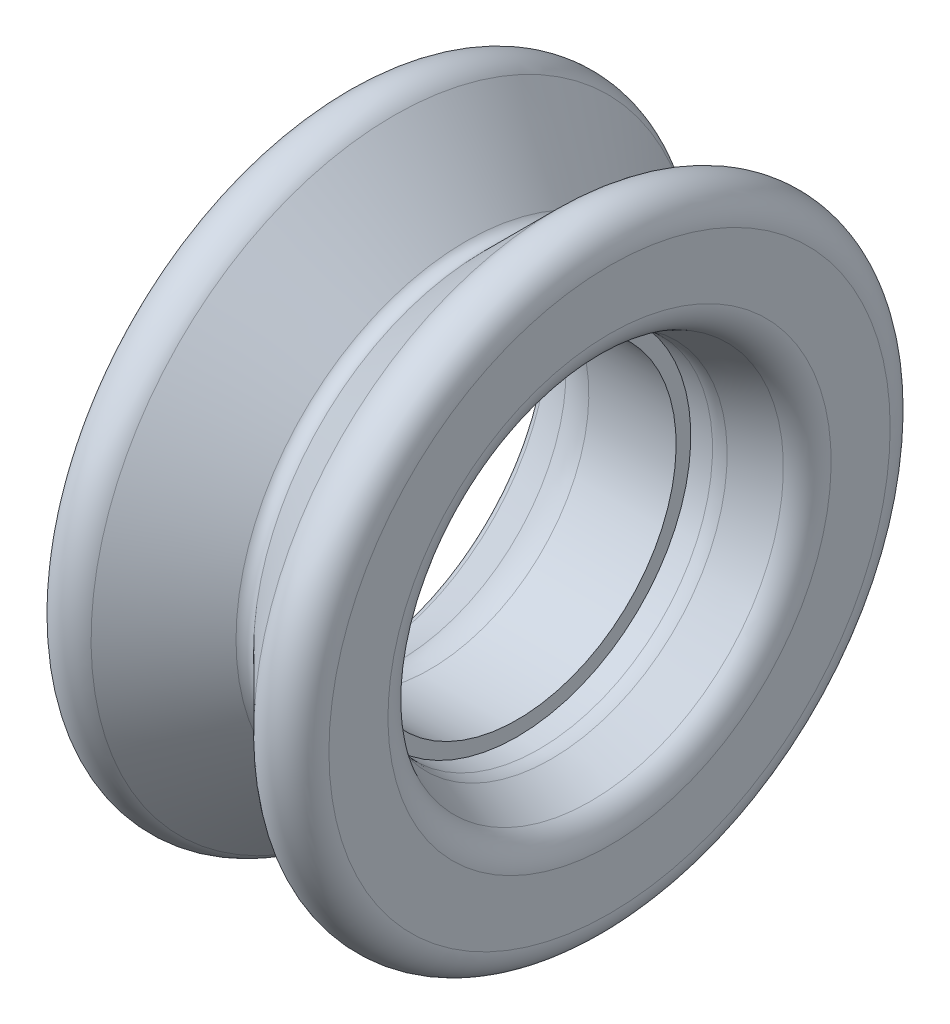
SolidWorks part; units mm, degrees
ref_plane "Front Plane" through (0, 0, 0) normal (0, 0, 1) x (1, 0, 0)
ref_plane "Top Plane" through (0, 0, 0) normal (0, 1, 0) x (1, 0, 0)
ref_plane "Right Plane" through (0, 0, 0) normal (1, 0, 0) x (0, 0, -1)
sketch "Sketch1" plane through (0, 0, 0) normal (0, 0, 1) x (1, 0, 0)
  line L0 (0, 0) -> (-4.699, 0) construction
  line L1 (-4.699, 6.35) -> (-1.016, 6.35) construction
  line L2 (-1.016, 6.35) -> (-1.016, 6.9469) construction
  line L3 (-1.016, 6.9469) -> (0, 6.9469) construction
  line L4 (-4.699, 6.477) -> (-1.143, 6.477)
  line L5 (-1.143, 6.477) -> (-1.143, 7.0739)
  line L6 (-1.143, 7.0739) -> (0, 7.0739)
  line L7 (-4.699, 6.35) -> (-4.699, -6.35) construction
  line L8 (-2.8575, 0) -> (-2.8575, 9.017) construction
  line L9 (-7.0666, 12.7) -> (1.3516, 12.7) construction
  line L11 (0.4535, 12.328) -> (-2.4983, 9.3762)
  line L12 (-3.2167, 9.3762) -> (-6.1685, 12.328)
  line L14 (-8.3366, 11.43) -> (-8.3366, 8.1842)
  line L15 (-8.3366, 8.1842) -> (-5.969, 6.8173)
  line L16 (0, 7.0739) -> (2.6216, 8.1842)
  line L17 (2.6216, 8.1842) -> (2.6216, 11.43)
  line L18 (1.3516, 11.43) -> (-7.0666, 11.43) construction
  line L19 (-4.699, 6.477) -> (-1.143, 6.477) construction
  arc A1 (0.4535, 12.328) -> (2.6216, 11.43) centre (1.3516, 11.43) cw
  arc A2 (-8.3366, 11.43) -> (-6.1685, 12.328) centre (-7.0666, 11.43) cw
  arc A3 (-3.2167, 9.3762) -> (-2.4983, 9.3762) centre (-2.8575, 9.7354) ccw
  arc A4 (-4.699, 6.477) -> (-5.969, 6.8173) centre (-4.699, 9.017) cw
  point P22 (-2.8575, 12.7)
  point P23 (-8.0555, 6.604)
  point P24 (-8.2096, 7.6214)
  point P31 (-2.8575, 11.43)
  point P32 (0, 0)
  point P33 (8.5774, 16.965)
  point P34 (-2.8575, 6.35)
  point P35 (0, 0)
  point P36 (1.3588, 7.912)
  point P38 (2.3394, 7.804)
  point P39 (2.4038, 10.9585)
  point P40 (0, 0)
  point P44 (2.4946, 7.874)
  point P45 (0, 0)
  point P46 (0, 0)
  point P47 (-8.1522, 7.8191)
  point P48 (0, 0)
  point P52 (-4.8336, 6.604)
  point P53 (0, 0)
  dimension "D6" = 1.27
  dimension "D7" = 0.508
  dimension "D8" = 2.54
  dimension "D3" = 12.7
  dimension "D4" = 90
  dimension "D2" = 2.54
  dimension "D5" = 30
  dimension "D1" = 0.127
revolve "Revolve1" add sketch "Sketch1" angle 360 about L0
fillet "Fillet3" radius 1.27 2 edges at (2.6216, 8.1842, 0) (-8.3366, 8.1842, 0)
fillet "Fillet4" radius 1.27 1 edges at (0, 7.0739, 0)
equation "\"bearingOffset\"=0.005"
equation "\"D1@Sketch1\"=\"bearingOffset\""
equation "\"minOD\"=0.652568"
equation "\"maxOR\"=0.71057"
equation "\"catchAngle\"=90"
equation "\"D4@Sketch1\"=\"catchAngle\""
